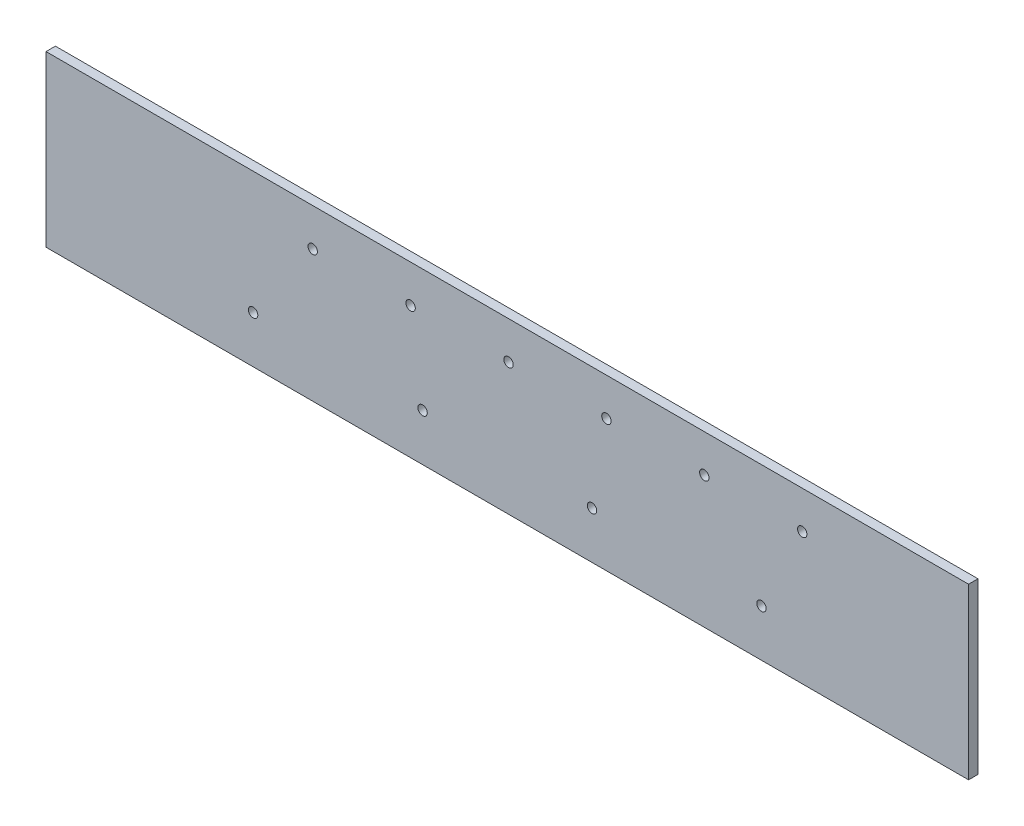
SolidWorks part; units mm, degrees
material "6061 Alloy"
ref_plane "Front Plane" through (0, 0, 0) normal (0, 0, 1) x (1, 0, 0)
ref_plane "Top Plane" through (0, 0, 0) normal (0, 1, 0) x (1, 0, 0)
ref_plane "Right Plane" through (0, 0, 0) normal (1, 0, 0) x (0, 0, -1)
sketch "Sketch1" plane through (0, 0, 457.2) normal (0, 0, 1) x (1, 0, 0)
  line L0 (311.15, 0) -> (311.15, 609.6) construction
  line L1 (-311.15, 114.3) -> (311.15, 114.3)
  line L2 (-311.15, 114.3) -> (-311.15, 0)
  line L3 (-311.15, 0) -> (311.15, 0)
  line L4 (311.15, 114.3) -> (311.15, 0)
  dimension "D1" = 114.3
extrude "Boss-Extrude1" add sketch "Sketch1" along normal blind 6.35
sketch "Sketch2" plane through (0, 0, 463.55) normal (0, 0, 1) x (1, 0, 0)
  point P0 (-131.2597, 88.9)
hole_wizard "1/4 (0.25) Diameter Hole1" positions "Sketch2" profile "Sketch3" hole size "1/4" standard "ANSI Inch" end condition through all
sketch "Sketch3" plane through (-131.2597, 88.9, 463.55) normal (1, 0, 0) x (0, -1, 0)
  line L0 (0, 0) -> (0, 6.35)
  line L1 (0, 6.35) -> (3.175, 6.35)
  line L2 (3.175, 6.35) -> (3.175, 0)
  line L5 (3.175, 0) -> (0, 0)
  line L11 (0, -6.35) -> (0, 107.95) construction
  dimension "Thru Hole Dia." = 6.35
  dimension "Thru Hole Depth" = 6.35
pattern_linear "LPattern1" count 6 spacing 66.04 along (1, 0, 0) of "1/4 (0.25) Diameter Hole1"
sketch "Sketch4" plane through (0, 0, 463.55) normal (0, 0, 1) x (1, 0, 0)
  point P0 (-171.45, 31.75)
hole_wizard "1/4 (0.25) Diameter Hole2" positions "Sketch4" profile "Sketch5" hole size "1/4" standard "ANSI Inch" end condition through all
sketch "Sketch5" plane through (-171.45, 31.75, 463.55) normal (1, 0, 0) x (0, -1, 0)
  line L0 (0, 0) -> (0, 6.35)
  line L1 (0, 6.35) -> (3.175, 6.35)
  line L2 (3.175, 6.35) -> (3.175, 0)
  line L5 (3.175, 0) -> (0, 0)
  line L11 (0, -6.35) -> (0, 107.95) construction
  dimension "Thru Hole Dia." = 6.35
  dimension "Thru Hole Depth" = 6.35
pattern_linear "LPattern2" count 4 spacing 114.3 along (1, 0, 0) of "1/4 (0.25) Diameter Hole2"
